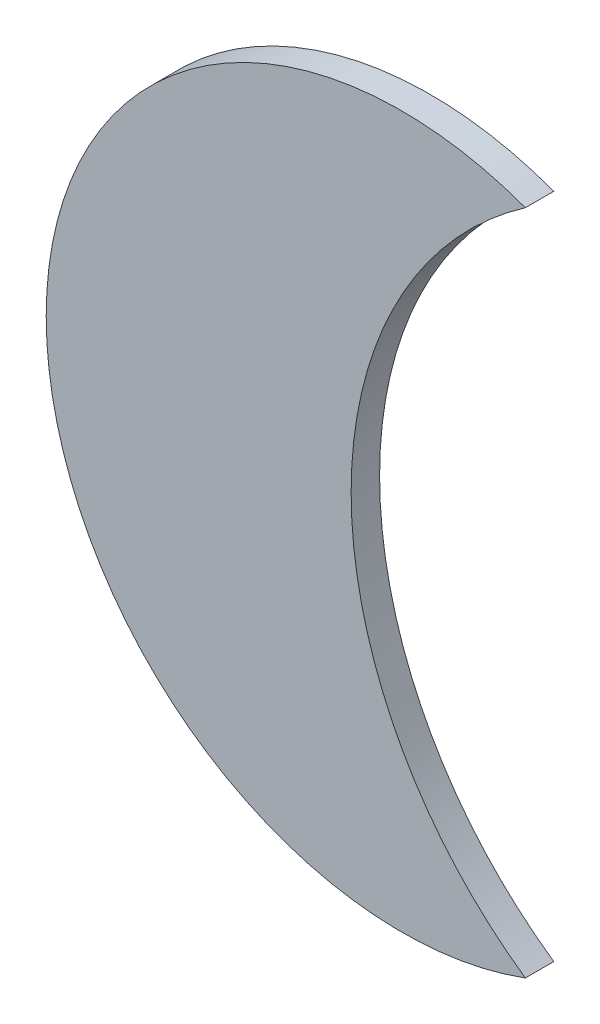
SolidWorks part; units mm, degrees
ref_plane "前视基准面" through (0, 0, 0) normal (0, 0, 1) x (1, 0, 0)
ref_plane "上视基准面" through (0, 0, 0) normal (0, 1, 0) x (1, 0, 0)
ref_plane "右视基准面" through (0, 0, 0) normal (1, 0, 0) x (0, 0, -1)
sketch "草图1" plane through (0, 0, 0) normal (0, 0, 1) x (1, 0, 0)
  arc A0 (86.7971, 234.4488) -> (86.7971, -234.4488) centre (0, 0) ccw
  arc A1 (86.7971, 234.4488) -> (86.7971, -234.4488) centre (250, 0) ccw
extrude "凸台-拉伸1" add sketch "草图1" along normal blind 20 contours A0 A1
